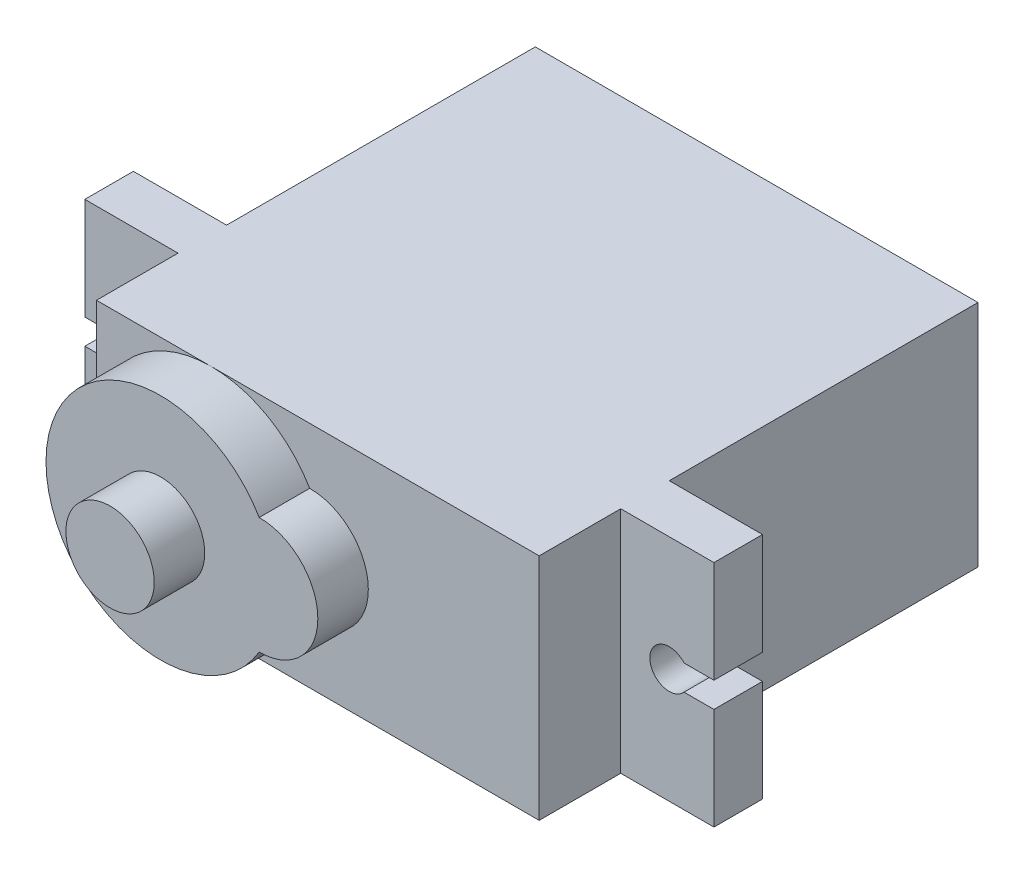
SolidWorks part; units mm, degrees
material "ABS"
ref_plane "Спереди" through (0, 0, 0) normal (0, 0, 1) x (1, 0, 0)
ref_plane "Сверху" through (0, 0, 0) normal (0, 1, 0) x (1, 0, 0)
ref_plane "Справа" through (0, 0, 0) normal (1, 0, 0) x (0, 0, -1)
sketch "Эскиз1" plane through (0, 0, 0) normal (0, 0, 1) x (1, 0, 0)
  line L1 (-11.4, 5.9) -> (11.4, 5.9)
  line L2 (-11.4, 5.9) -> (-11.4, -5.9)
  line L3 (-11.4, -5.9) -> (11.4, -5.9)
  line L4 (11.4, 5.9) -> (11.4, -5.9)
  line L5 (-11.4, 5.9) -> (11.4, -5.9) construction
  line L6 (-11.4, -5.9) -> (11.4, 5.9) construction
  point P0 (0, 0)
  dimension "D1" = 22.8
  dimension "D2" = 11.8
extrude "Бобышка-Вытянуть1" add sketch "Эскиз1" along normal blind 22.6
sketch "Эскиз2" plane through (0, 0, 22.6) normal (0, 0, 1) x (1, 0, 0)
  line L0 (-11.4, 0) -> (11.4, 0) construction
  line L1 (-11.4, 5.9) -> (-11.4, -5.9) construction
  line L2 (11.4, -5.9) -> (11.4, 5.9) construction
  circle A0 centre (-5.5, 0) radius 5.9
  dimension "D1" = 11.8
  dimension "D2" = 5.9
extrude "Бобышка-Вытянуть2" add sketch "Эскиз2" along normal blind 2.6
sketch "Эскиз3" plane through (0, 0, 25.2) normal (0, 0, 1) x (1, 0, 0)
  circle A0 centre (-5.5, 0) radius 2.275
  dimension "D1" = 4.55
extrude "Бобышка-Вытянуть3" add sketch "Эскиз3" along normal blind 2.6
sketch "Эскиз4" plane through (0, 0, 22.6) normal (0, 0, 1) x (1, 0, 0)
  line L3 (-5.5, -5.9) -> (11.4, -5.9)
  line L4 (11.4, -5.9) -> (11.4, 5.9)
  line L5 (11.4, 5.9) -> (-5.5, 5.9)
  line L6 (-5.5, -5.9) -> (11.4, -5.9)
  line L7 (11.4, -5.9) -> (11.4, 5.9)
  line L8 (11.4, 5.9) -> (-5.5, 5.9)
  arc A1 (-5.5, -5.9) -> (-5.5, 5.9) centre (-5.5, 0) ccw
  arc A2 (-5.5, -5.9) -> (-5.5, 5.9) centre (-5.5, 0) ccw
  circle A3 centre (-0.4, 0) radius 3
  dimension "D2" = 6
  dimension "D3" = 11.8
  dimension "D4" = 5.9
  dimension "D1" = 0
extrude "Бобышка-Вытянуть4" add sketch "Эскиз4" along normal blind 2.6 contours A2 A3
ref_plane "Плоскость1" through (0, 0, 15.9) normal (0, 0, -1) x (-1, 0, 0)
sketch "Эскиз5" plane through (0, 0, 15.9) normal (0, 0, -1) x (-1, 0, 0)
  line L0 (-16.2, 0) -> (16.2, 0) construction
  line L1 (16.2, 5.9) -> (-16.2, 5.9)
  line L2 (16.2, 5.9) -> (16.2, 0.65)
  line L3 (16.2, -5.9) -> (-16.2, -5.9)
  line L4 (-16.2, 5.9) -> (-16.2, 0.65)
  line L5 (16.2, 5.9) -> (-16.2, -5.9) construction
  line L6 (16.2, -5.9) -> (-16.2, 5.9) construction
  line L7 (-16.2, 0.65) -> (-14.6599, 0.65)
  line L8 (-16.2, -0.65) -> (-14.6599, -0.65)
  line L9 (-16.2, -0.65) -> (-16.2, -5.9)
  line L10 (16.2, 0.65) -> (14.6599, 0.65)
  line L11 (16.2, -0.65) -> (14.6599, -0.65)
  line L12 (16.2, -0.65) -> (16.2, -5.9)
  arc A0 (-14.6599, -0.65) -> (-14.6599, 0.65) centre (-13.9, 0) ccw
  arc A1 (14.6599, 0.65) -> (14.6599, -0.65) centre (13.9, 0) ccw
  point P0 (0, 0)
  dimension "D3" = 2
  dimension "D4" = 2
  dimension "D1" = 11.8
  dimension "D2" = 32.4
  dimension "D5" = 2.3
  dimension "D6" = 2.3
  dimension "D7" = 0.65
extrude "Бобышка-Вытянуть5" add sketch "Эскиз5" against normal blind 2.5
sketch "Эскиз6" plane through (-11.4, 0, 0) normal (-1, 0, 0) x (0, 0, 1)
  line L1 (4.5, 2) -> (6.1, 2)
  line L2 (4.5, 2) -> (4.5, -2)
  line L3 (4.5, -2) -> (6.1, -2)
  line L4 (6.1, 2) -> (6.1, -2)
  line L5 (4.5, 2) -> (6.1, -2) construction
  line L6 (4.5, -2) -> (6.1, 2) construction
  line L7 (15.9, 5.9) -> (0, 5.9) construction
  line L8 (0, 5.9) -> (0, -5.9) construction
  point P0 (5.3, 0)
  dimension "D1" = 4
  dimension "D2" = 1.6
  dimension "D3" = 4.5
  dimension "D4" = 5.9
extrude "Бобышка-Вытянуть6" add sketch "Эскиз6" along normal blind 1.5
fillet "Скругление1" radius 0.4 8 edges at (-12.9, -2, 5.3) (-12.9, 0, 4.5) (-12.9, 2, 5.3) (-12.9, 0, 6.1) (-12.15, 2, 4.5) (-12.15, -2, 4.5) (-12.15, 2, 6.1) (-12.15, -2, 6.1)
